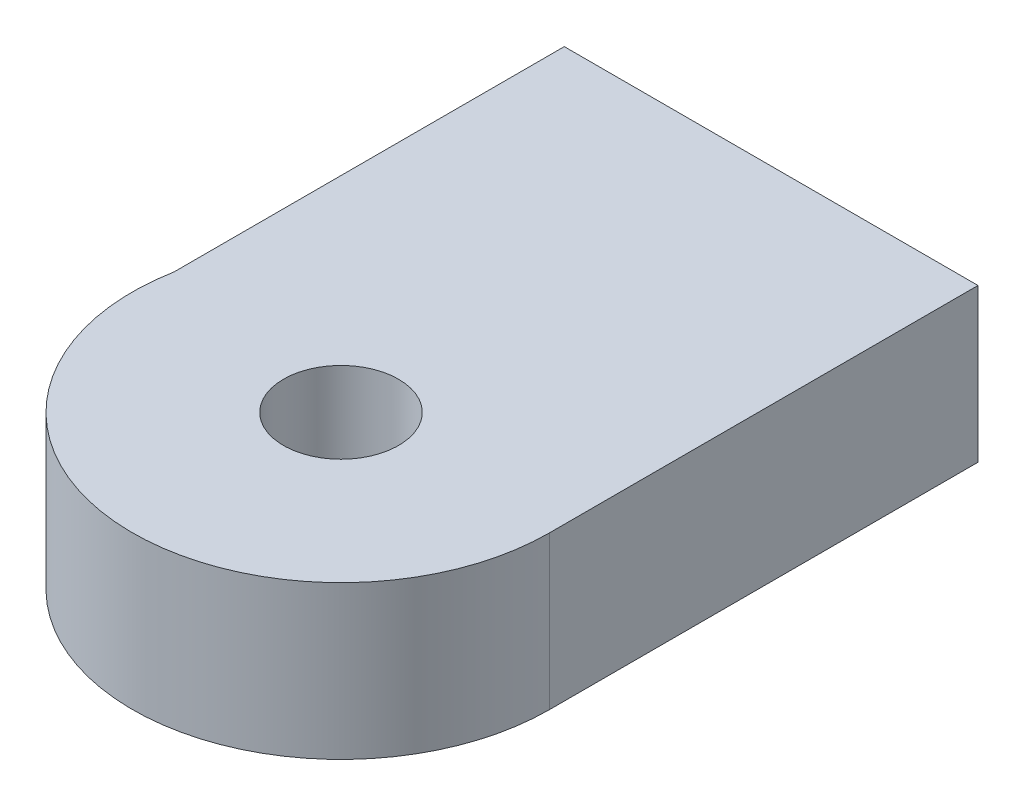
SolidWorks part; units mm, degrees
ref_plane "Front Plane" through (0, 0, 0) normal (0, 0, 1) x (1, 0, 0)
ref_plane "Top Plane" through (0, 0, 0) normal (0, 1, 0) x (1, 0, 0)
ref_plane "Right Plane" through (0, 0, 0) normal (1, 0, 0) x (0, 0, -1)
sketch "Sketch2" plane through (0, -2111.3899, 0) normal (0, 1, 0) x (1, 0, 0)
  circle A1 centre (-53.694, 163.8403) radius 12.7
extrude "Boss-Extrude6" add sketch "Sketch2" along normal blind 40.64
sketch "Sketch3" plane through (0, -2070.7499, 0) normal (0, 1, 0) x (1, 0, 0)
  circle A0 centre (-53.694, 163.8403) radius 3.5
  dimension "D1" = 7
extrude "Cut-Extrude1" cut sketch "Sketch3" against normal up to surface (40.64 mm away) up to face at (-66.394, -2111.3899, -163.8403)
sketch "Sketch4" plane through (0, -2111.3899, 0) normal (0, -1, 0) x (1, 0, 0)
  circle A0 centre (-61.9429, -159.0778) radius 1.778
  circle A2 centre (-53.694, -173.3653) radius 1.778
  circle A3 centre (-45.4451, -159.0778) radius 1.778
extrude "Cut-Extrude2" cut sketch "Sketch4" against normal blind 6
sketch "Sketch7" plane through (0, -2111.3899, 0) normal (0, -1, 0) x (1, 0, 0)
  line L9 (-40.994, -163.8403) -> (-40.994, -182.6343)
  line L10 (-40.994, -182.6343) -> (-66.1797, -182.6343)
  line L11 (-66.1797, -166.1636) -> (-66.1797, -182.6343)
  circle A0 centre (-53.694, -163.8403) radius 12.7 construction
  arc A1 (-66.1797, -166.1636) -> (-40.994, -163.8403) centre (-53.694, -163.8403) ccw
extrude "Boss-Extrude8" add sketch "Sketch7" against normal blind 10
sketch "Sketch8" plane through (0, 0, -182.6343) normal (0, 0, -1) x (-1, 0, 0)
  line L0 (40.994, -2101.3899) -> (40.994, -2111.3899) construction
  line L1 (40.994, -2101.3899) -> (66.1797, -2101.3899)
  line L2 (40.994, -2101.3899) -> (40.994, -2111.3899)
  line L3 (40.994, -2111.3899) -> (66.1797, -2111.3899)
  line L4 (66.1797, -2101.3899) -> (66.1797, -2111.3899)
  line L5 (66.1797, -2101.3899) -> (40.994, -2101.3899) construction
  line L6 (66.1797, -2111.3899) -> (40.994, -2111.3899) construction
  line L7 (66.1797, -2101.3899) -> (66.1797, -2111.3899) construction
extrude "Boss-Extrude9" add sketch "Sketch8" along normal up to surface (7.2848 mm away)
sketch "Sketch9" plane through (0, -2070.7499, 0) normal (0, 1, 0) x (1, 0, 0)
  line L0 (-40.994, 189.9191) -> (-40.994, 163.8403) construction
  line L2 (-66.1797, 163.8403) -> (-66.1797, 189.9191)
  line L3 (-66.1797, 189.9191) -> (-40.994, 189.9191)
  line L4 (-40.994, 163.8403) -> (-40.994, 189.9191)
  line L5 (-66.1797, 166.1636) -> (-66.1797, 189.9191) construction
  arc A0 (-40.994, 163.8403) -> (-66.1797, 163.8403) centre (-53.5868, 163.8403) ccw
extrude "Boss-Extrude10" add sketch "Sketch9" against normal up to surface (30.64 mm away) up to face at (-53.322, -2101.3899, -180.3317)
hole_wizard "CSK for M3 Flat Head Machine Screw1" positions "Sketch14" profile "Sketch15" countersink size "M3" standard "ANSI Metric"
sketch "Sketch14" plane through (0, 0, -189.9191) normal (0, 0, -1) x (-1, 0, 0)
  point P10 (53.5868, -2075.7499)
  point P12 (62.6264, -2075.7499)
  point P14 (44.5473, -2075.7499)
sketch "Sketch15" plane through (-53.5868, -2075.7499, -189.9191) normal (1, 0, 0) x (0, 1, 0)
  line L0 (0, 0) -> (0, 10)
  line L1 (0, 10) -> (1.7, 8.9785)
  line L2 (1.7, 8.9785) -> (1.7, 1.45)
  line L3 (1.7, 1.45) -> (3.15, 0)
  line L5 (3.15, 0) -> (0, 0)
  line L6 (-1.7, 1.45) -> (-3.15, 0) construction
  line L10 (0, 10) -> (-1.7, 8.9785) construction
  line L11 (0, -6.35) -> (0, 107.95) construction
  dimension "Hole Dia." = 3.4
  dimension "Hole Depth" = 10
  dimension "Near C'Sink Dia." = 6.3
  dimension "Near C'Sink Angle" = 90
  dimension "Drill Angle" = 118
ref_plane "Plane1" through (0, -2091.0699, 0) normal (0, 1, 0) x (1, 0, 0)
mirror "Mirror1" about plane through (0, -2091.0699, 0) normal (0, 1, 0) of "CSK for M3 Flat Head Machine Screw1"
sketch "Sketch25" plane through (0, 0, -189.9191) normal (0, 0, -1) x (-1, 0, 0)
  line L0 (40.994, -2111.3899) -> (40.994, -2070.7499) construction
  line L1 (40.994, -2102.0691) -> (67.7131, -2102.0691)
  line L2 (40.994, -2102.0691) -> (40.994, -2070.7499)
  line L3 (40.994, -2070.7499) -> (67.7131, -2070.7499)
  line L4 (67.7131, -2102.0691) -> (67.7131, -2070.7499)
extrude "Cut-Extrude9" cut sketch "Sketch25" against normal through all
